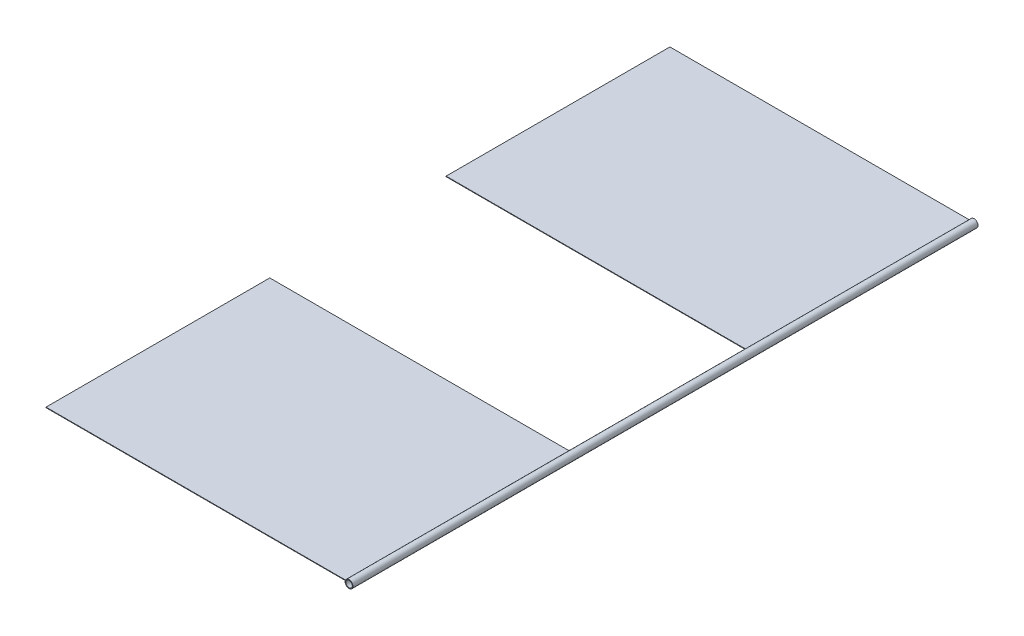
SolidWorks part; units mm, degrees
material "PVC Rigid"
ref_plane "Front Plane" through (0, 0, 0) normal (0, 0, 1) x (1, 0, 0)
ref_plane "Top Plane" through (0, 0, 0) normal (0, 1, 0) x (1, 0, 0)
ref_plane "Right Plane" through (0, 0, 0) normal (1, 0, 0) x (0, 0, -1)
sketch "Sketch1" plane through (0, 0, 0) normal (0, 0, 1) x (1, 0, 0)
  circle A0 centre (0, 0) radius 19.05
  circle A2 centre (0, 0) radius 15.875
  dimension "D1" = 38.1
  dimension "D2" = 31.75
extrude "Boss-Extrude1" add sketch "Sketch1" along normal blind 3048
sketch "Sketch2" plane through (0, 0, 0) normal (1, 0, 0) x (0, 0, -1)
  circle A0 centre (-1828.8, 0) radius 12.7
  dimension "D1" = 25.4
  dimension "D2" = 1219.2
extrude "Cut-Extrude1" cut sketch "Sketch2" against normal through all
sketch "Sketch3" plane through (0, 0, 0) normal (0, 1, 0) x (1, 0, 0)
  line L0 (-15.875, 0) -> (-15.875, -1816.1) construction
  line L1 (-15.875, 0) -> (-1483.4557, 0)
  line L2 (-15.875, 0) -> (-15.875, -1091.2098)
  line L3 (-15.875, -1091.2098) -> (-1483.4557, -1091.2098)
  line L4 (-1483.4557, 0) -> (-1483.4557, -1091.2098)
  line L5 (-24.1935, -3108.7542) -> (-24.1935, 66.465) construction
  line L6 (295.4289, -1521.1446) -> (-179.4492, -1521.1446) construction
  line L7 (-15.875, -1951.0794) -> (-1483.4557, -1951.0794)
  line L8 (-1483.4557, -3042.2892) -> (-1483.4557, -1951.0794)
  line L9 (-15.875, -3042.2892) -> (-1483.4557, -3042.2892)
  line L10 (-15.875, -3042.2892) -> (-15.875, -1951.0794)
extrude "Boss-Extrude2" add sketch "Sketch3" along normal blind 2.54
sketch "Sketch4" plane through (0, 2.54, 0) normal (0, 1, 0) x (1, 0, 0)
  line L0 (-1158.5243, -620.7561) -> (-1631.7736, -620.7561) construction
  line L1 (-289.3952, -2563.4664) -> (-289.3952, -2754.133) construction
